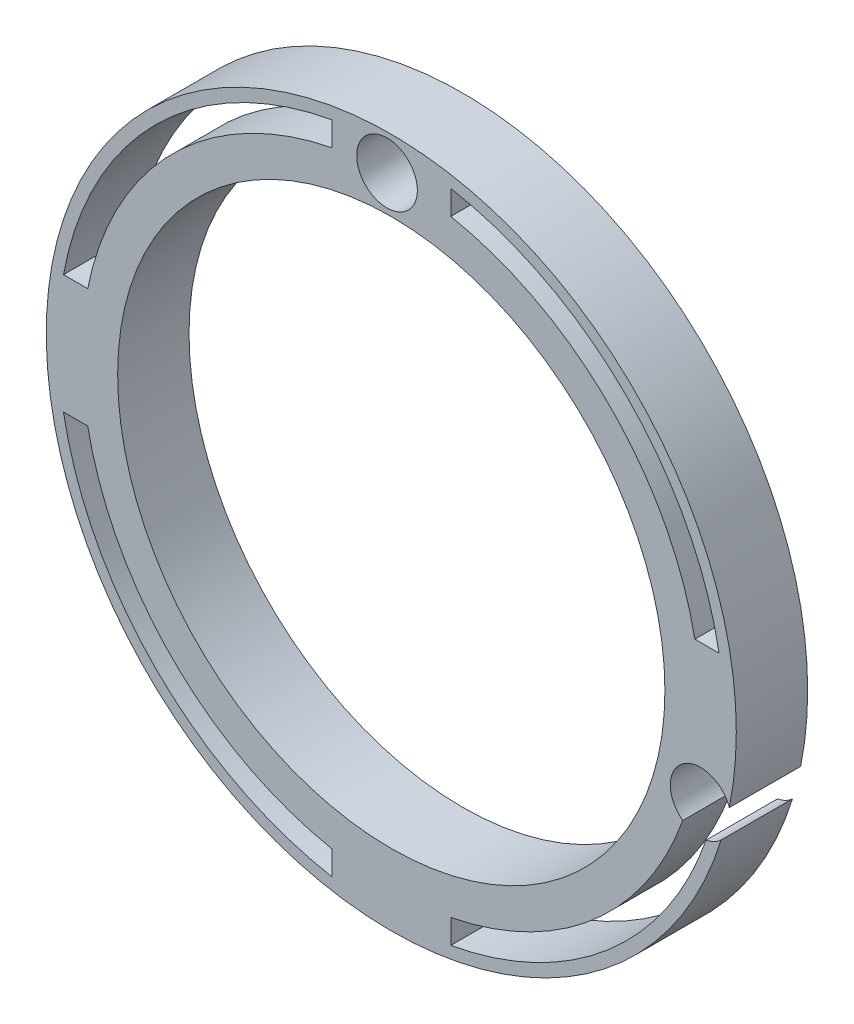
SolidWorks part; units mm, degrees
material "Copper"
ref_plane "Front Plane" through (0, 0, 0) normal (0, 0, 1) x (1, 0, 0)
ref_plane "Top Plane" through (0, 0, 0) normal (0, 1, 0) x (1, 0, 0)
ref_plane "Right Plane" through (0, 0, 0) normal (1, 0, 0) x (0, 0, -1)
ref_plane "Plane1" through (259.3015, 0, 0) normal (-1, 0, 0) x (0, 0, 1)
sketch "Sketch2" plane through (259.3015, 0, 0) normal (-1, 0, 0) x (0, 0, 1)
  line L0 (0, -124.0737) -> (0, -125.5737)
  line L1 (0, -119.5737) -> (6, -119.5737)
  line L2 (0, -119.5737) -> (0, -121.0737)
  line L3 (0, -125.5737) -> (6, -125.5737)
  line L4 (6, -119.5737) -> (6, -125.5737)
  line L5 (0, -121.0737) -> (2, -121.0737)
  line L7 (0, -124.0737) -> (2, -124.0737)
  line L8 (2, -121.0737) -> (2, -124.0737)
  line L9 (6, -122.5737) -> (-2.3896, -122.5737) construction
  line L10 (22.865, -148.5737) -> (53.0055, -148.5737) construction
  dimension "D1" = 3
  dimension "D2" = 2
  dimension "D3" = 6
  dimension "D4" = 6
  dimension "D5" = 1.5
  dimension "D6" = 29
revolve "Revolve1" add sketch "Sketch2" angle 360 about L10
sketch "Sketch3" plane through (0, 0, 6) normal (0, 0, 1) x (1, 0, 0)
  line L0 (185.4881, -148.5737) -> (328.4429, -148.5737) construction
  line L1 (196.5327, -143.5737) -> (254.3015, -143.5737) construction
  line L3 (196.5327, -153.5737) -> (254.3015, -153.5737) construction
  line L6 (254.3015, -97.5994) -> (254.3015, -143.5737) construction
  line L8 (264.3015, -97.5994) -> (264.3015, -143.5737) construction
  line L9 (259.3015, -89.2638) -> (259.3015, -228.676) construction
  line L10 (259.3015, 55) -> (259.3015, -55) construction
  line L11 (254.3015, -153.5737) -> (254.3015, -216.1727) construction
  line L12 (264.3015, -143.5737) -> (323.6499, -143.5737) construction
  line L13 (264.3015, -153.5737) -> (323.6499, -153.5737) construction
  line L14 (264.3015, -153.5737) -> (264.3015, -216.1727) construction
  line L15 (254.3015, -174.0884) -> (254.3015, -176.1237)
  line L16 (264.3015, -174.0884) -> (264.3015, -176.1237)
  line L17 (286.8515, -153.5737) -> (284.8162, -153.5737)
  line L18 (286.8515, -143.5737) -> (284.8162, -143.5737)
  line L19 (264.3015, -121.0237) -> (264.3015, -123.059)
  line L20 (254.3015, -121.0237) -> (254.3015, -123.059)
  line L21 (233.7868, -143.5737) -> (231.7516, -143.5737)
  line L22 (233.7868, -153.5737) -> (231.7516, -153.5737)
  arc A0 (254.3015, -123.059) -> (233.7868, -143.5737) centre (259.3015, -148.5737) ccw
  arc A1 (231.7516, -153.5737) -> (254.3015, -176.1237) centre (259.3015, -148.5737) ccw
  arc A2 (233.7868, -153.5737) -> (254.3015, -174.0884) centre (259.3015, -148.5737) ccw
  arc A3 (254.3015, -121.0237) -> (231.7516, -143.5737) centre (259.3015, -148.5737) ccw
  arc A4 (286.8515, -143.5737) -> (264.3015, -121.0237) centre (259.3015, -148.5737) ccw
  arc A5 (284.8162, -143.5737) -> (264.3015, -123.059) centre (259.3015, -148.5737) ccw
  arc A6 (264.3015, -176.1237) -> (286.8515, -153.5737) centre (259.3015, -148.5737) ccw
  arc A7 (264.3015, -174.0884) -> (284.8162, -153.5737) centre (259.3015, -148.5737) ccw
  dimension "D1" = 26
  dimension "D2" = 28
  dimension "D3" = 5
  dimension "D4" = 5
  dimension "D5" = 5
  dimension "D6" = 5
extrude "Cut-Extrude1" cut sketch "Sketch3" against normal through all
sketch "Sketch4" plane through (0, 0, 6) normal (0, 0, 1) x (1, 0, 0)
  circle A0 centre (258.9447, -122.5737) radius 2.55
  circle A1 centre (259.3015, -148.5737) radius 23 construction
  circle A2 centre (259.3015, -148.5737) radius 26.0024 construction
  circle A3 centre (285.3015, -155.2168) radius 2.55
  circle A4 centre (252.6584, -181.5737) radius 2.55
  circle A5 centre (226.3015, -148.9306) radius 2.55
  point P4 (259.3015, -148.5737)
  point P17 (255.8015, -152.0737)
  dimension "D1" = 5.1
  dimension "D3" = 4
  dimension "D2" = 26
extrude "Cut-Extrude2" cut sketch "Sketch4" against normal through all
equation "\"D5@Sketch2\"=\"D1@Sketch2\"/2"
equation "\"D5@Sketch3\"=\"D3@Sketch3\""
equation "\"D6@Sketch3\"=\"D5@Sketch3\""
equation "\"slit_thickness\" = 1"
equation "\"D2@Sketch3\"=\"D1@Sketch3\"+2"
